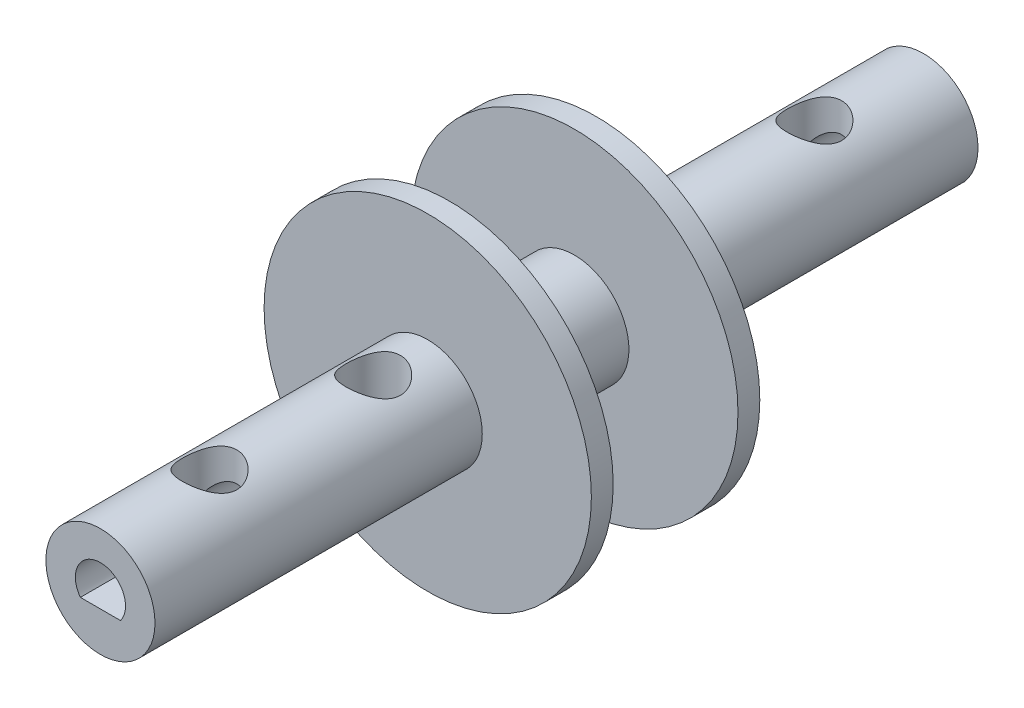
SolidWorks part; units mm, degrees
ref_plane "Front Plane" through (0, 0, 0) normal (0, 0, 1) x (1, 0, 0)
ref_plane "Top Plane" through (0, 0, 0) normal (0, 1, 0) x (1, 0, 0)
ref_plane "Right Plane" through (0, 0, 0) normal (1, 0, 0) x (0, 0, -1)
sketch "Sketch1" plane through (0, 0, 0) normal (0, 0, 1) x (1, 0, 0)
  circle A0 centre (0, 0) radius 6.35
extrude "Boss-Extrude1" add sketch "Sketch1" along normal blind 95.8088
sketch "Sketch2" plane through (0, 0, 95.8088) normal (0, 0, 1) x (1, 0, 0)
  line L0 (0, 2.921) -> (0, -1.7526) construction
  line L1 (-2.3368, -1.7526) -> (2.3368, -1.7526)
  arc A0 (2.3368, -1.7526) -> (-2.3368, -1.7526) centre (0, 0) ccw
  arc A1 (2.3368, -1.7526) -> (-2.3368, -1.7526) centre (0, 0) ccw
  dimension "D1" = 5.842
  dimension "D2" = 4.6736
sketch "Sketch4" plane through (0, 0, 0) normal (0, 1, 0) x (1, 0, 0)
  line L0 (0, -95.8088) -> (0, -83.1088)
  line L1 (-6.35, -95.8088) -> (6.35, -95.8088) construction
  line L2 (0, 0) -> (0, -12.7)
  line L3 (6.35, 0) -> (-6.35, 0) construction
  line L4 (0, -83.1088) -> (0, -64.0588) construction
  line L5 (0, -12.7) -> (0, -31.75)
  circle A0 centre (0, -83.1088) radius 3.175
  circle A1 centre (0, -12.7) radius 3.175
  circle A2 centre (0, -64.0588) radius 3.175
  circle A3 centre (0, -31.75) radius 3.175
  dimension "D1" = 6.35
  dimension "D2" = 6.35
  dimension "D4" = 19.05
  dimension "D3" = 12.7
  dimension "D5" = 19.05
  dimension "D6" = 12.7
extrude "Cut-Extrude2" cut sketch "Sketch4" against normal through all both and the other way through all
ref_plane "Plane1" through (0, 0, 57.7088) normal (0, 0, 1) x (1, 0, 0)
sketch "Sketch5" plane through (0, 0, 57.7088) normal (0, 0, 1) x (1, 0, 0)
  circle A0 centre (0, 0) radius 19.05
  dimension "D1" = 38.1
extrude "Boss-Extrude2" add sketch "Sketch5" against normal blind 2.54
ref_plane "Plane2" through (0, 0, 38.1) normal (0, 0, -1) x (-1, 0, 0)
sketch "Sketch6" plane through (0, 0, 38.1) normal (0, 0, -1) x (-1, 0, 0)
  circle A0 centre (0, 0) radius 19.05
  dimension "D1" = 38.1
extrude "Boss-Extrude3" add sketch "Sketch6" against normal blind 2.54
extrude "Cut-Extrude4" cut sketch "Sketch2" against normal blind 27.94 contours L0 A1 L1 | A0 L0 L1
sketch "Sketch7" plane through (0, 0, 0) normal (0, 0, -1) x (-1, 0, 0)
  line L0 (2.921, 0) -> (-1.7526, 0) construction
  line L2 (-1.7526, -2.3368) -> (-1.7526, 2.3368)
  circle A0 centre (0, 0) radius 2.921
  dimension "D1" = 5.842
  dimension "D3" = 4.6736
extrude "Cut-Extrude5" cut sketch "Sketch7" against normal blind 27.94 contours L0 A0 L2 | A0 L0 L2
